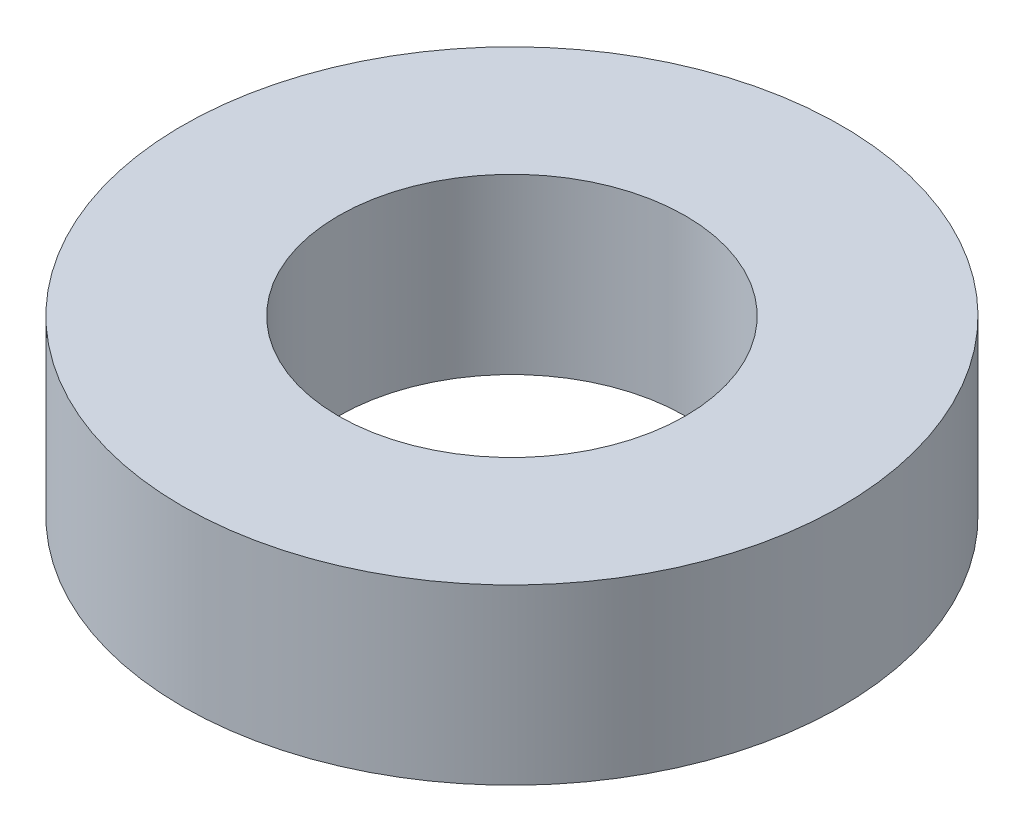
SolidWorks part; units mm, degrees
ref_plane "Front Plane" through (0, 0, 0) normal (0, 0, 1) x (1, 0, 0)
ref_plane "Top Plane" through (0, 0, 0) normal (0, 1, 0) x (1, 0, 0)
ref_plane "Right Plane" through (0, 0, 0) normal (1, 0, 0) x (0, 0, -1)
sketch "Sketch1" plane through (0, 0, 0) normal (0, 1, 0) x (1, 0, 0)
  circle A0 centre (0, 0) radius 5
  circle A1 centre (0, 0) radius 9.5
  dimension "D1" = 10
  dimension "D2" = 19
extrude "Boss-Extrude1" add sketch "Sketch1" along normal blind 5
